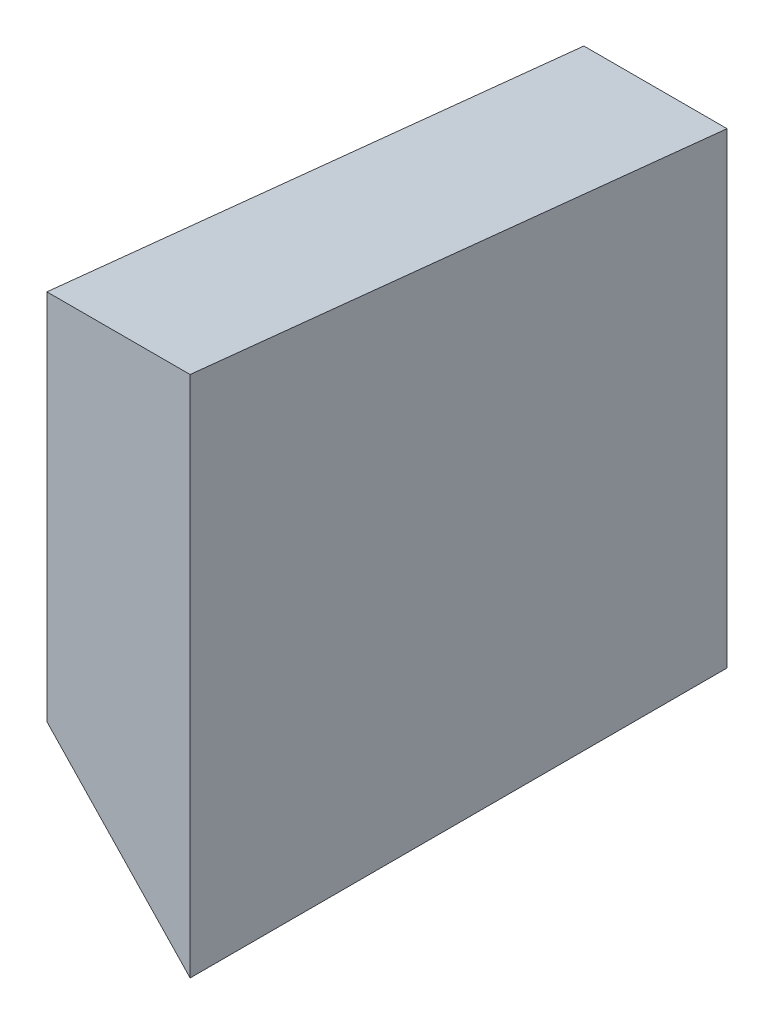
SolidWorks part; units mm, degrees
ref_plane "Plan de face" through (0, 0, 0) normal (0, 0, 1) x (1, 0, 0)
ref_plane "Plan de dessus" through (0, 0, 0) normal (0, 1, 0) x (1, 0, 0)
ref_plane "Plan de droite" through (0, 0, 0) normal (1, 0, 0) x (0, 0, -1)
sketch "Esquisse1" plane through (0, 0, 0) normal (0, 1, 0) x (1, 0, 0)
  line L1 (-2.54, 0) -> (2.54, 0)
  line L2 (-2.54, 0) -> (-2.54, -19.05)
  line L3 (-2.54, -19.05) -> (2.54, -19.05)
  line L4 (2.54, 0) -> (2.54, -19.05)
  point P4 (0, 0)
  dimension "D1" = 5.08
  dimension "D2" = 19.05
extrude "Boss.-Extru.1" add sketch "Esquisse1" against normal blind 20.828
sketch "Esquisse2" plane through (2.54, 0, 0) normal (1, 0, 0) x (0, 0, -1)
  line L3 (0, -1.972) -> (-19.05, 0)
  line L4 (0, -20.828) -> (0, 0) construction
  line L5 (-19.05, 0) -> (0, 0)
  line L6 (0, 0) -> (0, -1.972)
  line L7 (-19.05, 0) -> (0, 0) construction
  dimension "D1" = 84.09
extrude "Enlèv. mat.-Extru.1" cut sketch "Esquisse2" against normal through all
sketch "Esquisse3" plane through (0, 0, 19.05) normal (0, 0, 1) x (1, 0, 0)
  line L0 (-2.54, -20.828) -> (-2.54, -13.208)
  line L5 (-2.54, -13.208) -> (2.54, -18.542)
  line L6 (2.54, -20.828) -> (2.54, 0) construction
  line L7 (-2.54, -20.828) -> (-2.54, 0) construction
  line L11 (2.54, -18.542) -> (2.54, -20.828)
  line L12 (2.54, -20.828) -> (-2.54, -20.828)
  dimension "D1" = 2.286
  dimension "D2" = 7.62
extrude "Enlèv. mat.-Extru.2" cut sketch "Esquisse3" against normal through all
